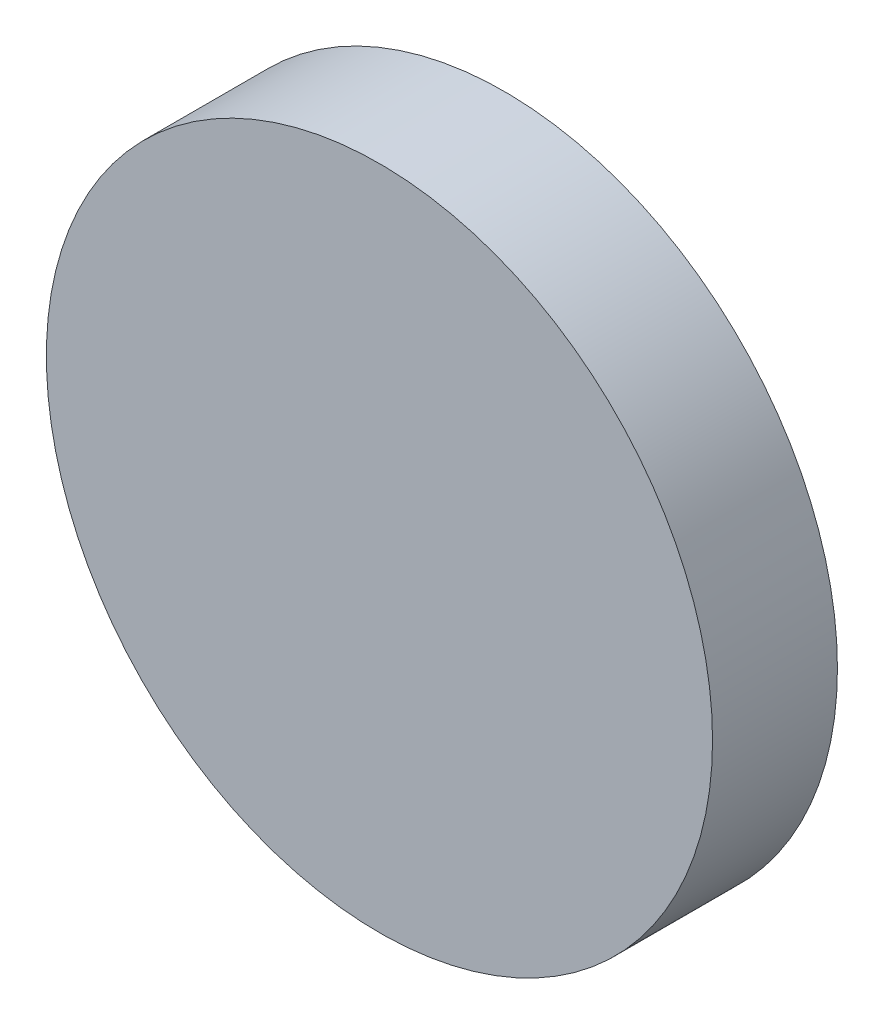
SolidWorks part; units mm, degrees
ref_plane "Front Plane" through (0, 0, 0) normal (0, 0, 1) x (1, 0, 0)
ref_plane "Top Plane" through (0, 0, 0) normal (0, 1, 0) x (1, 0, 0)
ref_plane "Right Plane" through (0, 0, 0) normal (1, 0, 0) x (0, 0, -1)
sketch "Sketch1" plane through (0, 0, 0) normal (0, 0, 1) x (1, 0, 0)
  circle A0 centre (0, 0) radius 8
extrude "Boss-Extrude1" add sketch "Sketch1" along normal blind 3
